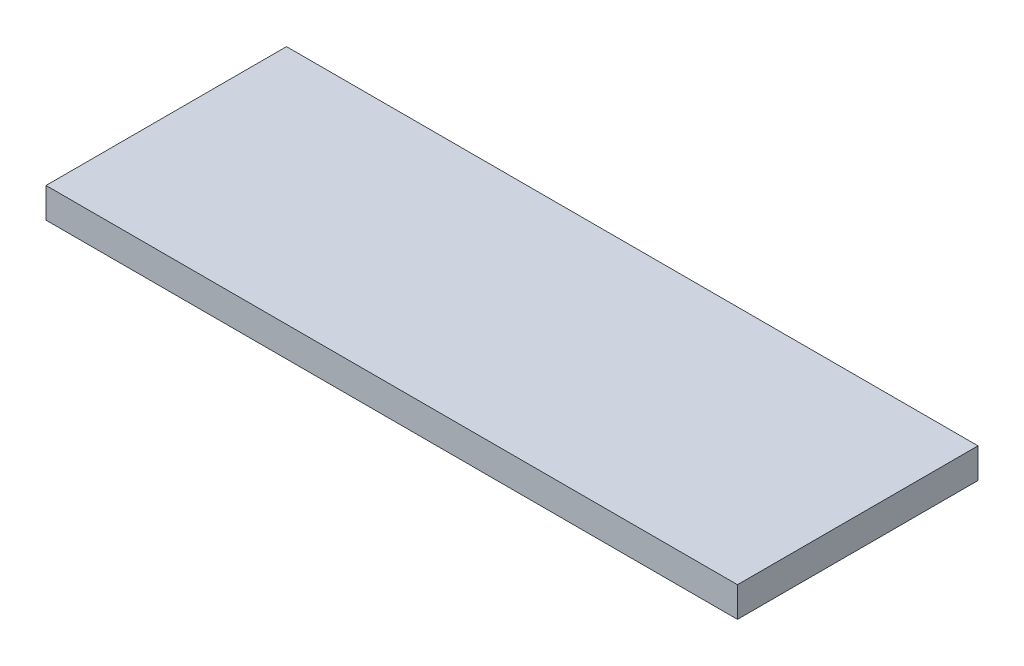
SolidWorks part; units mm, degrees
ref_plane "Front Plane" through (0, 0, 0) normal (0, 0, 1) x (1, 0, 0)
ref_plane "Top Plane" through (0, 0, 0) normal (0, 1, 0) x (1, 0, 0)
ref_plane "Right Plane" through (0, 0, 0) normal (1, 0, 0) x (0, 0, -1)
sketch "Sketch1" plane through (0, 0, 0) normal (0, 1, 0) x (1, 0, 0)
  line L0 (-105.5872, 0) -> (214.4484, 0) construction
  line L1 (-57.5, 20) -> (57.5, 20)
  line L2 (-57.5, 20) -> (-57.5, -20)
  line L3 (-57.5, -20) -> (57.5, -20)
  line L4 (57.5, 20) -> (57.5, -20)
  line L5 (0, 151.0142) -> (0, -135.4626) construction
  dimension "D1" = 115
  dimension "D2" = 40
extrude "Boss-Extrude1" add sketch "Sketch1" along normal blind 5
